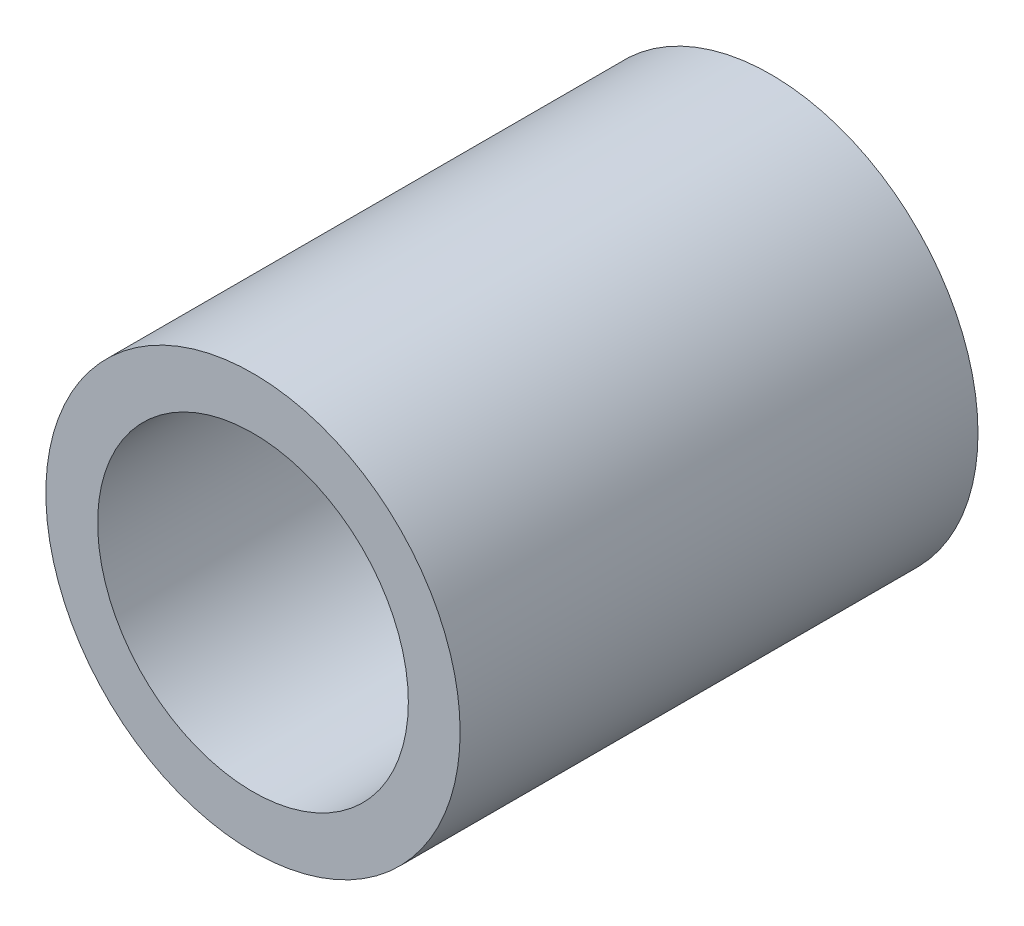
SolidWorks part; units mm, degrees
ref_plane "Front Plane" through (0, 0, 0) normal (0, 0, 1) x (1, 0, 0)
ref_plane "Top Plane" through (0, 0, 0) normal (0, 1, 0) x (1, 0, 0)
ref_plane "Right Plane" through (0, 0, 0) normal (1, 0, 0) x (0, 0, -1)
sketch "Sketch2" plane through (0, 0, 0) normal (0, 0, 1) x (1, 0, 0)
  circle A0 centre (0, 0) radius 4
  circle A1 centre (0, 0) radius 3
  dimension "D1" = 8
  dimension "D2" = 6
extrude "Boss-Extrude1" add sketch "Sketch2" along normal blind 10
